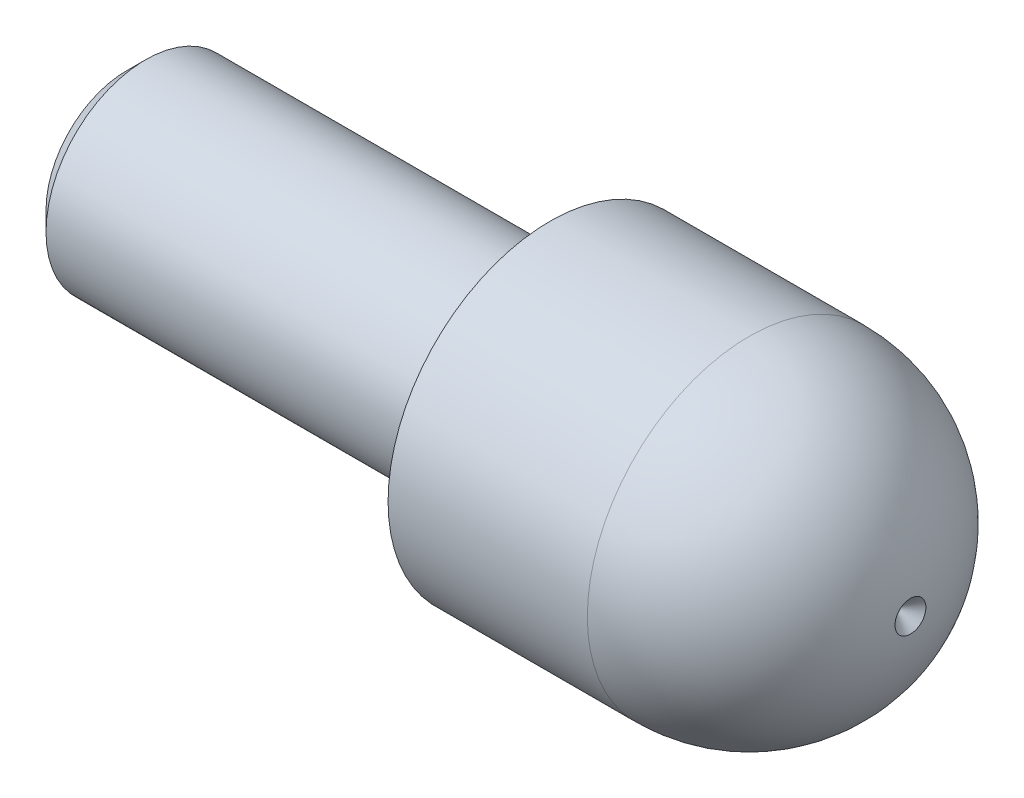
SolidWorks part; units mm, degrees
material "AISI 4340 Steel, normalized"
ref_plane "Front Plane" through (0, 0, 0) normal (0, 0, 1) x (1, 0, 0)
ref_plane "Top Plane" through (0, 0, 0) normal (0, 1, 0) x (1, 0, 0)
ref_plane "Right Plane" through (0, 0, 0) normal (1, 0, 0) x (0, 0, -1)
ref_plane "Plane1" through (0, 0, 0) normal (0, 0, 1) x (1, 0, 0)
sketch "Sketch1" plane through (0, 0, 0) normal (0, 0, 1) x (1, 0, 0)
  line L0 (-17, 0) -> (-17, 3.233)
  line L1 (-17, 3.233) -> (-16.233, 4)
  line L2 (-16.233, 4) -> (0, 4)
  line L3 (0, 4) -> (0, 0)
  line L4 (0, 0) -> (-17, 0)
  line L5 (0, 0) -> (-17, 0) construction
revolve "Revolve1" add sketch "Sketch1" angle 360 about L5
cosmetic thread "Cosmetic Thread1" parameters "D1"=12, "D2"=6.891
ref_plane "Plane2" through (0, 0, 0) normal (0, 0, 1) x (1, 0, 0)
sketch "Sketch2" plane through (0, 0, 0) normal (0, 0, 1) x (1, 0, 0)
  line L0 (0, 0) -> (0, 6.5)
  line L1 (0, 6.5) -> (8, 6.5)
  line L2 (14.4703, 0.6203) -> (13.85, 0)
  line L3 (13.85, 0) -> (0, 0)
  line L4 (50, 0) -> (-50, 0) construction
  arc A0 (8, 6.5) -> (14.4703, 0.6203) centre (8, 0) cw
revolve "Revolve2" add sketch "Sketch2" angle 360 about L4
ref_plane "Plane3" through (0, 0, 0) normal (0, 0, 1) x (1, 0, 0)
sketch "Sketch3" plane through (0, 0, 0) normal (0, 0, 1) x (1, 0, 0)
  line L0 (-0.8268, 3.9) -> (-0.1732, 3.9)
  line L1 (0, 4) -> (0, 4.9)
  line L2 (0, 4.9) -> (-1, 4.9)
  line L3 (-1, 4.9) -> (-1, 4)
  line L4 (0, 0) -> (-1, 0) construction
  arc A0 (-1, 4) -> (-0.8268, 3.9) centre (-0.8268, 4.1) ccw
  arc A1 (-0.1732, 3.9) -> (0, 4) centre (-0.1732, 4.1) ccw
revolve "Cut-Revolve1" cut sketch "Sketch3" angle 360 about L4
